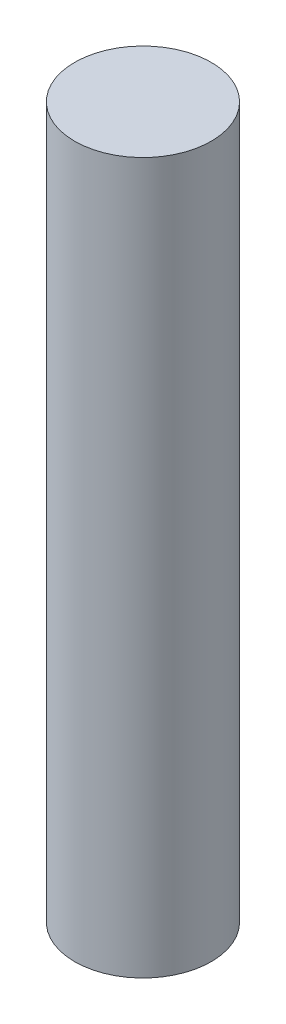
SolidWorks part; units mm, degrees
ref_plane "Front Plane" through (0, 0, 0) normal (0, 0, 1) x (1, 0, 0)
ref_plane "Top Plane" through (0, 0, 0) normal (0, 1, 0) x (1, 0, 0)
ref_plane "Right Plane" through (0, 0, 0) normal (1, 0, 0) x (0, 0, -1)
sketch "Sketch1" plane through (0, 0, 0) normal (0, 1, 0) x (1, 0, 0)
  circle A0 centre (0, 0) radius 1.25
  dimension "D1" = 2.5
extrude "Boss-Extrude1" add sketch "Sketch1" along normal blind 13
